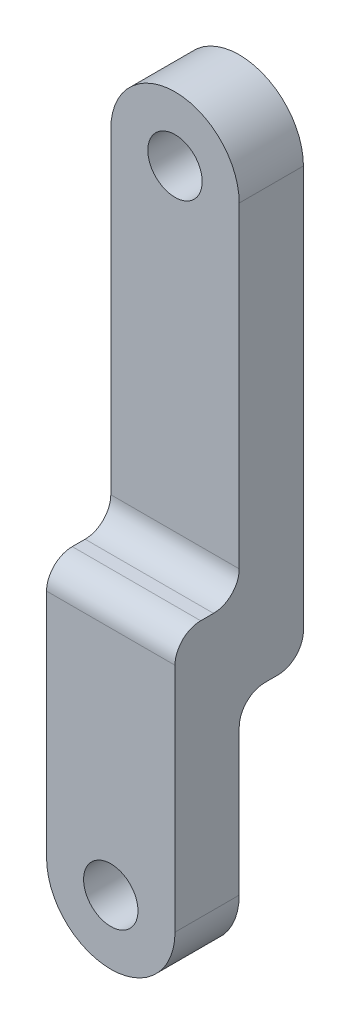
SolidWorks part; units mm, degrees
ref_plane "Front Plane" through (0, 0, 0) normal (0, 0, 1) x (1, 0, 0)
ref_plane "Top Plane" through (0, 0, 0) normal (0, 1, 0) x (1, 0, 0)
ref_plane "Right Plane" through (0, 0, 0) normal (1, 0, 0) x (0, 0, -1)
sketch "Sketch1" plane through (0, 0, 0) normal (0, 0, 1) x (1, 0, 0)
  line L0 (7.5, 70) -> (7.5, 0)
  line L1 (-7.5, 0) -> (-7.5, 70)
  arc A0 (-7.5, 0) -> (7.5, 0) centre (0, 0) ccw
  arc A1 (7.5, 70) -> (-7.5, 70) centre (0, 70) ccw
  circle A2 centre (0, 70) radius 3.175
  circle A3 centre (0, 0) radius 3.175
  dimension "D1" = 7.5
  dimension "D3" = 6.35
  dimension "D2" = 70
extrude "Boss-Extrude1" add sketch "Sketch1" along normal blind 15
sketch "Sketch2" plane through (0, 0, 15) normal (0, 0, 1) x (1, 0, 0)
  line L0 (-7.5, 30) -> (7.5, 30)
  line L1 (-7.5, 70) -> (-7.5, 0) construction
  line L2 (7.5, 0) -> (7.5, 70) construction
  line L3 (-7.5, 70) -> (-7.5, 30)
  line L4 (7.5, 30) -> (7.5, 70)
  arc A0 (7.5, 70) -> (-7.5, 70) centre (0, 70) ccw construction
  arc A1 (7.5, 70) -> (-7.5, 70) centre (0, 70) ccw
  dimension "D1" = 30
extrude "Cut-Extrude1" cut sketch "Sketch2" against normal blind 7.5
sketch "Sketch3" plane through (0, 0, 0) normal (0, 0, -1) x (-1, 0, 0)
  line L0 (-7.5, 0) -> (-7.5, 70) construction
  line L1 (7.5, 70) -> (7.5, 0) construction
  line L2 (-7.5, 0) -> (-7.5, 20)
  line L3 (7.5, 20) -> (7.5, 0)
  line L4 (-7.5, 20) -> (7.5, 20)
  line L5 (7.5, 30) -> (-7.5, 30) construction
  arc A0 (-7.5, 0) -> (7.5, 0) centre (0, 0) ccw construction
  arc A1 (-7.5, 0) -> (7.5, 0) centre (0, 0) ccw
  dimension "D1" = 10
extrude "Cut-Extrude2" cut sketch "Sketch3" against normal blind 7.5
fillet "Fillet1" radius 3 4 edges at (0, 20, 7.5) (0, 30, 7.5) (0, 30, 15) (0, 20, 0)
